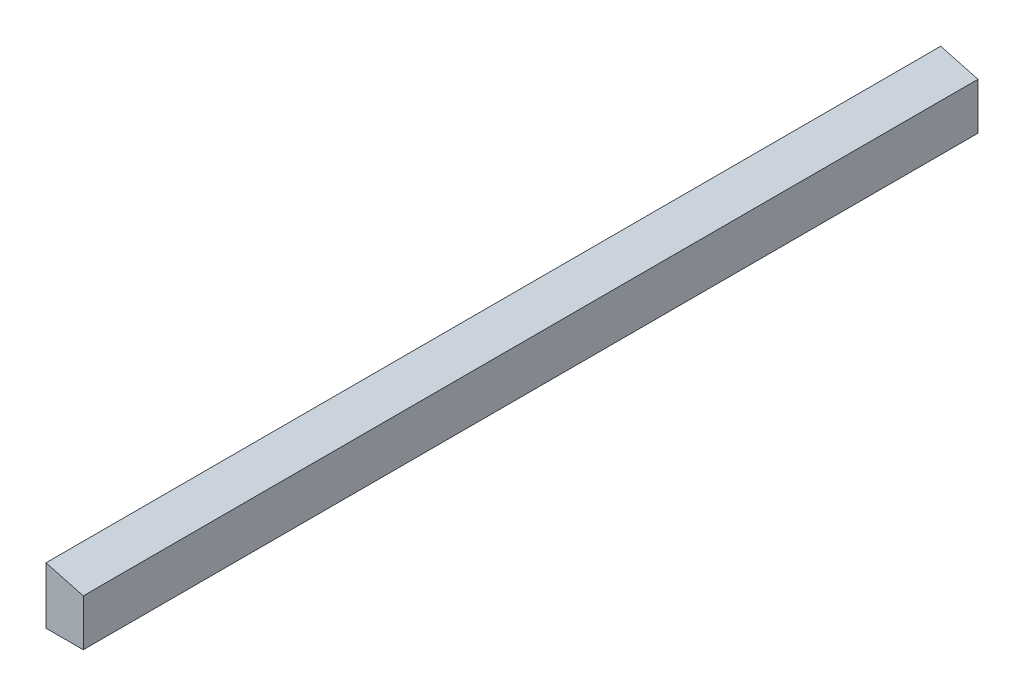
SolidWorks part; units mm, degrees
material "Pine"
ref_plane "Front Plane" through (0, 0, 0) normal (0, 0, 1) x (1, 0, 0)
ref_plane "Top Plane" through (0, 0, 0) normal (0, 1, 0) x (1, 0, 0)
ref_plane "Right Plane" through (0, 0, 0) normal (1, 0, 0) x (0, 0, -1)
sketch "Sketch1" plane through (0, 0, 0) normal (0, 0, 1) x (1, 0, 0)
  line L0 (-15.0827, 35.2896) -> (23.0173, 25.0807)
  line L2 (-15.0827, 35.2896) -> (-15.0827, -22.6542)
  line L3 (-15.0827, -22.6542) -> (23.0173, -22.6542)
  line L4 (23.0173, 25.0807) -> (23.0173, -22.6542)
  dimension "D1" = 75
  dimension "D2" = 57.9437
  dimension "D3" = 38.1
extrude "Boss-Extrude1" add sketch "Sketch1" along normal blind 914.4
